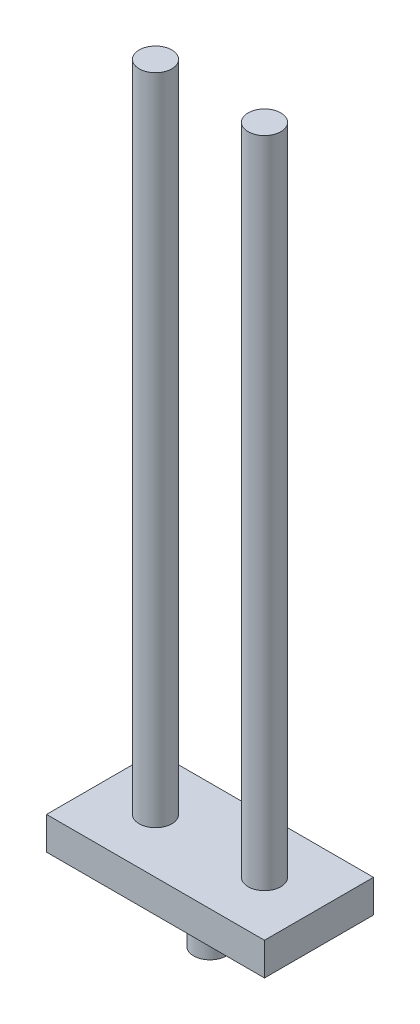
SolidWorks part; units mm, degrees
ref_plane "Front Plane" through (0, 0, 0) normal (0, 0, 1) x (1, 0, 0)
ref_plane "Top Plane" through (0, 0, 0) normal (0, 1, 0) x (1, 0, 0)
ref_plane "Right Plane" through (0, 0, 0) normal (1, 0, 0) x (0, 0, -1)
sketch "Sketch1" plane through (0, 0, 0) normal (0, 1, 0) x (1, 0, 0)
  line L0 (0, 5) -> (0, -5) construction
  line L1 (-10, 5) -> (10, 5)
  line L2 (-10, 5) -> (-10, -5)
  line L3 (-10, -5) -> (10, -5)
  line L4 (10, 5) -> (10, -5)
  line L5 (-10, 5) -> (10, -5) construction
  line L6 (-10, -5) -> (10, 5) construction
  line L7 (10, 0) -> (-10, 0) construction
  point P0 (0, 0)
  dimension "D1" = 10
  dimension "D2" = 20
extrude "Boss-Extrude1" add sketch "Sketch1" along normal blind 3
sketch "Sketch2" plane through (0, 3, 0) normal (0, 1, 0) x (1, 0, 0)
  line L0 (-10, 0) -> (10, 0) construction
  line L1 (-10, 5) -> (-10, -5) construction
  line L2 (10, -5) -> (10, 5) construction
  line L3 (0, 5) -> (0, -5) construction
  line L4 (10, 5) -> (-10, 5) construction
  line L5 (-10, -5) -> (10, -5) construction
  circle A0 centre (-5, 0) radius 1.5
  circle A1 centre (5, 0) radius 1.5
  dimension "D1" = 3
  dimension "D2" = 5
extrude "Boss-Extrude2" add sketch "Sketch2" along normal blind 60
sketch "Sketch3" plane through (0, 0, 0) normal (0, -1, 0) x (1, 0, 0)
  line L0 (0, 5) -> (0, -5) construction
  line L1 (-10, 5) -> (10, 5) construction
  line L2 (10, -5) -> (-10, -5) construction
  line L3 (-10, 0) -> (10, 0) construction
  line L4 (-10, -5) -> (-10, 5) construction
  line L5 (10, 5) -> (10, -5) construction
  circle A0 centre (0, 0) radius 1.5
  dimension "D1" = 3
extrude "Boss-Extrude3" add sketch "Sketch3" along normal blind 5
sketch "Sketch4" plane through (0, -5, 0) normal (0, -1, 0) x (1, 0, 0)
  line L1 (-2.5, 2.5) -> (2.5, 2.5)
  line L2 (-2.5, 2.5) -> (-2.5, -2.5)
  line L3 (-2.5, -2.5) -> (2.5, -2.5)
  line L4 (2.5, 2.5) -> (2.5, -2.5)
  line L5 (-2.5, 2.5) -> (2.5, -2.5) construction
  line L6 (-2.5, -2.5) -> (2.5, 2.5) construction
  point P0 (0, 0)
  dimension "D1" = 5
  dimension "D2" = 5
extrude "Boss-Extrude4" [suppressed] add sketch "Sketch4" along normal blind 10
sketch "Sketch5" plane through (0, 3, 0) normal (0, 1, 0) x (1, 0, 0)
  point P0 (5, 0)
  point P1 (-5, 0)
  point P3 (0, 0)
